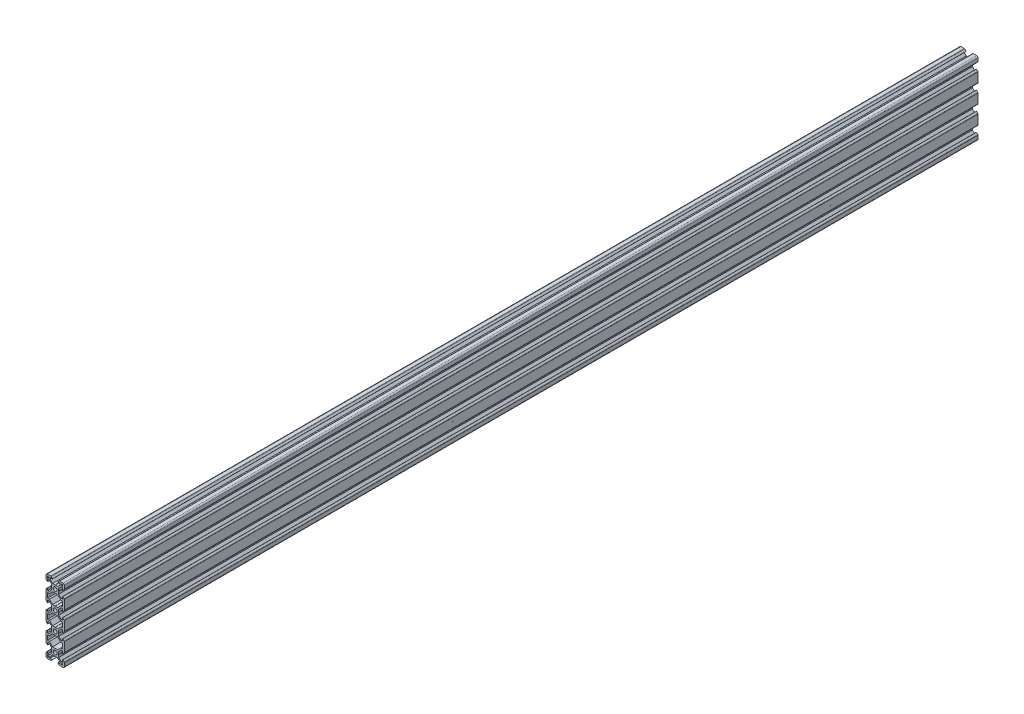
SolidWorks part; units mm, degrees
ref_plane "Front Plane" through (0, 0, 0) normal (0, 0, 1) x (1, 0, 0)
ref_plane "Top Plane" through (0, 0, 0) normal (0, 1, 0) x (1, 0, 0)
ref_plane "Right Plane" through (0, 0, 0) normal (1, 0, 0) x (0, 0, -1)
sketch "Sketch2" plane through (0, 0, 0) normal (0, 0, 1) x (1, 0, 0)
  line L0 (-8.2, 2.8875) -> (-8.2, 5.4975)
  line L3 (-4.9072, 9.9975) -> (-8.5, 9.9975)
  line L4 (-10, 4.9047) -> (-10, 8.4975)
  line L5 (-2.1, 0) -> (-3.8, 0) construction
  line L6 (0, 3.8) -> (0, 2.1) construction
  line L7 (-0.1, 3.9) -> (-2.8404, 3.9)
  line L8 (-3.9, 0.1) -> (-3.9, 2.8383)
  line L9 (-2.89, 8.1975) -> (-5.5, 8.1975)
  line L10 (-6.57, 8.1975) -> (-6.57, 7.6575)
  line L11 (-8.2, 6.5675) -> (-7.66, 6.5675)
  line L12 (-5.5, 8.1975) -> (-5.5, 6.5588)
  line L13 (-6.56, 5.4975) -> (-8.2, 5.4975)
  line L14 (-8.2, 8.1975) -> (-1.4852, 1.4847) construction
  line L15 (-6.56, 5.4975) -> (-3.9, 2.8383)
  line L16 (-5.5, 6.5588) -> (-2.8404, 3.9)
  line L17 (-7.66, 6.5675) -> (-6.57, 7.6575)
  line L18 (-8.7302, 7.6671) -> (-0.5302, -0.5304) construction
  line L19 (-7.6698, 8.7279) -> (0.5302, 0.5304) construction
  line L20 (-8.2, 8.1975) -> (0, 0) construction
  line L21 (-8.2, 6.5675) -> (-8.2, 8.1975)
  line L22 (-8.2, -0.0025) -> (-8.2, 8.1975) construction
  line L23 (-6.57, 8.1975) -> (-8.2, 8.1975)
  line L24 (0, 8.1975) -> (-8.2, 8.1975) construction
  line L25 (-10, -0.0025) -> (-10, 9.9975) construction
  line L26 (0, 9.9975) -> (-10, 9.9975) construction
  line L27 (-2.89, 8.3075) -> (-2.89, 8.1975)
  line L29 (-8.31, 2.8875) -> (-8.2, 2.8875)
  line L30 (-4.3486, 9.7661) -> (-2.89, 8.3075)
  line L31 (-8.31, 2.8875) -> (-9.7686, 4.3461)
  line L34 (-0.1, 3.9) -> (0, 3.8)
  line L35 (-3.9, 0.1) -> (-3.8, 0)
  line L36 (-10, -20) -> (0, -20) construction
  line L37 (0, 0) -> (0, -20) construction
  line L38 (0, -3.9) -> (-2.8404, -3.9)
  line L39 (-3.8, 0) -> (-3.9, -0.1)
  line L40 (-3.9, -0.1) -> (-3.9, -2.84)
  line L41 (-2.8404, -3.9) -> (-6.25, -7.3096)
  line L42 (-3.9, -2.84) -> (-6.56, -5.5)
  line L43 (-8.21, -2.89) -> (-8.21, -5.5)
  line L44 (-6.56, 5.4975) -> (-6.56, -5.5) construction
  line L45 (-6.56, -5.5) -> (-8.21, -5.5)
  line L46 (-6.25, -7.3096) -> (-6.25, -12.7) construction
  line L47 (-6.25, -7.3096) -> (-8.21, -7.3096)
  line L48 (-8.21, -2.89) -> (-8.31, -2.89)
  line L49 (-8.31, -2.89) -> (-9.7657, -4.3457)
  line L51 (-8.21, -7.3096) -> (-8.21, -12.7)
  line L52 (-0.1, -16.1) -> (-2.85, -16.1)
  line L53 (-3.9, -17.16) -> (-3.9, -19.9)
  line L54 (-6.25, -12.7) -> (-2.85, -16.1)
  line L58 (-3.9, -17.16) -> (-6.56, -14.5)
  line L60 (-8.21, -17.11) -> (-8.31, -17.11)
  line L61 (-10, -4.9114) -> (-10, -15.0886)
  line L62 (-9.7657, -15.6543) -> (-8.31, -17.11)
  line L63 (-0.1, -16.1) -> (0, -16.2)
  line L64 (-3.9, -19.9) -> (-3.8, -20)
  line L65 (-8.21, -14.5) -> (-6.56, -14.5)
  line L66 (-8.21, -12.7) -> (-6.25, -12.7)
  line L67 (-10, -30.01) -> (0, -30.01) construction
  line L68 (-8.21, -14.5) -> (-8.21, -17.11)
  line L69 (-3.9, -20.1) -> (-3.8, -20)
  line L71 (-10, -20) -> (0, -20) construction
  line L72 (-8.21, -30.01) -> (-8.21, -27.31)
  line L73 (-10, -30.01) -> (-10, -24.9101)
  line L74 (-8.21, -25.4987) -> (-8.21, -22.8887)
  line L76 (-8.21, -27.31) -> (-6.25, -27.31)
  line L77 (-8.21, -25.4987) -> (-6.56, -25.4987)
  line L85 (-0.1, -23.9) -> (0, -23.8)
  line L95 (-9.7657, -24.3444) -> (-8.31, -22.8887)
  line L96 (-8.21, -22.8887) -> (-8.31, -22.8887)
  line L97 (-3.9, -22.8387) -> (-6.56, -25.4987)
  line L98 (-6.25, -27.31) -> (-2.84, -23.9)
  line L99 (-3.9, -22.8387) -> (-3.9, -20.1)
  line L100 (-0.1, -23.9) -> (-2.84, -23.9)
  arc A1 (-10, 8.4975) -> (-8.5, 9.9975) centre (-8.5, 8.4975) cw
  arc A2 (-9.7686, 4.3461) -> (-10, 4.9047) centre (-9.21, 4.9047) cw
  arc A3 (-4.3486, 9.7661) -> (-4.9072, 9.9975) centre (-4.9072, 9.2075) ccw
  arc A5 (0, 2.1) -> (0, -2.1) centre (0, 0) ccw
  arc A6 (-9.7657, -15.6543) -> (-10, -15.0886) centre (-9.2, -15.0886) cw
  arc A7 (-9.7657, -4.3457) -> (-10, -4.9114) centre (-9.2, -4.9114) ccw
  arc A8 (0, -17.9) -> (0, -22.1) centre (0, -20) ccw
  arc A10 (-9.7657, -24.3444) -> (-10, -24.9101) centre (-9.2, -24.9101) ccw
  point P29 (-10, 9.9975)
  point P39 (-10, 4.5775)
  point P42 (-4.58, 9.9975)
  point P76 (-10, -15.42)
  point P79 (-10, -4.58)
  dimension "D15" = 1.5
  dimension "D22" = 0.79
  dimension "D30" = 2.1
  dimension "D31" = 2.1
  dimension "D51" = 0.8
  dimension "D52" = 2.61
  dimension "D64" = 1.65
  dimension "D53" = 0.8
  dimension "D55" = 3.9
  dimension "D4" = 1.8
  dimension "D5" = 3.43
  dimension "D6" = 3.43
  dimension "D7" = 0.54
  dimension "D8" = 0.54
  dimension "D9" = 1.07
  dimension "D10" = 1.07
  dimension "D11" = 3.9
  dimension "D12" = 3.9
  dimension "D16" = 7.11
  dimension "D17" = 0.11
  dimension "D18" = 1.69
  dimension "D19" = 0.11
  dimension "D20" = 7.11
  dimension "D21" = 1.69
  dimension "D23" = 10
  dimension "D24" = 0.1
  dimension "D25" = 45
  dimension "D26" = 0.1
  dimension "D27" = 45
  dimension "D28" = 1.64
  dimension "D29" = 20
  dimension "D32" = 3.9
  dimension "D33" = 45
  dimension "D34" = 2.74
  dimension "D35" = 45
  dimension "D36" = 1.96
  dimension "D37" = 2.61
  dimension "D38" = 90
  dimension "D39" = 2.61
  dimension "D40" = 3.9
  dimension "D41" = 3.9
  dimension "D42" = 135
  dimension "D44" = 45
  dimension "D45" = 1.8
  dimension "D46" = 0.1
  dimension "D47" = 0.1
  dimension "D48" = 45
  dimension "D49" = 0.1
  dimension "D50" = 45
  dimension "D43" = 5.5
  dimension "D54" = 3.9
  dimension "D56" = 45
  dimension "D57" = 2.7
  dimension "D59" = 45
  dimension "D60" = 0.1
  dimension "D61" = 0.1
  dimension "D62" = 45
  dimension "D63" = 2.84
  dimension "D65" = 1.96
  dimension "D66" = 45
  dimension "D67" = 1.5
  dimension "D13" = 0.75
  dimension "D14" = 0.75
sketch "Sketch3" plane through (0, 0, 0) normal (0, 0, 1) x (1, 0, 0)
  line L0 (-0.1, 3.9) -> (0, 3.8) construction
  line L1 (-0.1, 3.9) -> (-2.8404, 3.9) construction
  line L2 (-5.5, 6.5588) -> (-2.8404, 3.9) construction
  line L3 (-5.5, 8.1975) -> (-5.5, 6.5588) construction
  line L4 (-2.89, 8.1975) -> (-5.5, 8.1975) construction
  line L5 (-7.66, 6.5675) -> (-6.57, 7.6575)
  line L6 (-6.57, 7.6575) -> (-6.57, 8.1975)
  line L7 (-6.57, 8.1975) -> (-8.2, 8.1975)
  line L8 (-8.2, 8.1975) -> (-8.2, 6.5675)
  line L9 (-8.2, 6.5675) -> (-7.66, 6.5675)
  line L10 (-7.66, 6.5675) -> (-6.57, 7.6575)
  line L11 (-6.57, 7.6575) -> (-6.57, 8.1975)
  line L12 (-6.57, 8.1975) -> (-8.2, 8.1975)
  line L13 (-8.2, 8.1975) -> (-8.2, 6.5675)
  line L14 (-8.2, 6.5675) -> (-7.66, 6.5675)
  line L15 (-2.89, 8.3075) -> (-2.89, 8.1975) construction
  line L16 (-4.3486, 9.7661) -> (-2.89, 8.3075) construction
  line L17 (-4.9072, 9.9975) -> (-8.5, 9.9975) construction
  line L18 (-10, 4.9047) -> (-10, 8.4975) construction
  line L19 (-8.31, 2.8875) -> (-9.7686, 4.3461) construction
  line L20 (-8.31, 2.8875) -> (-8.2, 2.8875) construction
  line L21 (-8.2, 2.8875) -> (-8.2, 5.4975) construction
  line L22 (-6.56, 5.4975) -> (-8.2, 5.4975) construction
  line L23 (-6.56, 5.4975) -> (-3.9, 2.8383) construction
  line L24 (-3.9, 0.1) -> (-3.9, 2.8383) construction
  line L25 (-3.9, 0.1) -> (-3.8, 0) construction
  line L26 (-3.8, 0) -> (-3.9, -0.1) construction
  line L27 (-3.9, -0.1) -> (-3.9, -2.84) construction
  line L28 (-3.9, -2.84) -> (-6.56, -5.5) construction
  line L29 (-6.56, -5.5) -> (-8.21, -5.5) construction
  line L30 (-8.21, -2.89) -> (-8.21, -5.5) construction
  line L31 (-8.21, -2.89) -> (-8.31, -2.89) construction
  line L32 (-8.31, -2.89) -> (-9.7657, -4.3457) construction
  line L33 (-10, -4.9114) -> (-10, -15.0886) construction
  line L34 (-9.7657, -15.6543) -> (-8.31, -17.11) construction
  line L35 (-8.21, -17.11) -> (-8.31, -17.11) construction
  line L36 (-8.21, -14.5) -> (-8.21, -17.11) construction
  line L37 (-8.21, -14.5) -> (-6.56, -14.5) construction
  line L38 (-3.9, -17.16) -> (-6.56, -14.5) construction
  line L39 (-3.9, -17.16) -> (-3.9, -19.9) construction
  line L40 (-3.9, -19.9) -> (-3.8, -20) construction
  line L41 (-3.9, -20.1) -> (-3.8, -20) construction
  line L42 (-3.9, -22.8387) -> (-3.9, -20.1) construction
  line L43 (-3.9, -22.8387) -> (-6.56, -25.4987) construction
  line L44 (-8.21, -25.4987) -> (-6.56, -25.4987) construction
  line L45 (-8.21, -25.4987) -> (-8.21, -22.8887) construction
  line L46 (-8.21, -22.8887) -> (-8.31, -22.8887) construction
  line L47 (-9.7657, -24.3444) -> (-8.31, -22.8887) construction
  line L48 (-10, -30.01) -> (-10, -24.9101) construction
  line L49 (0, -3.9) -> (-2.8404, -3.9) construction
  line L50 (-2.8404, -3.9) -> (-6.25, -7.3096) construction
  line L51 (-6.25, -7.3096) -> (-8.21, -7.3096) construction
  line L52 (-8.21, -7.3096) -> (-8.21, -12.7) construction
  line L53 (-8.21, -12.7) -> (-6.25, -12.7) construction
  line L54 (-6.25, -12.7) -> (-2.85, -16.1) construction
  line L55 (-0.1, -16.1) -> (-2.85, -16.1) construction
  line L56 (-0.1, -16.1) -> (0, -16.2) construction
  line L57 (-0.1, -23.9) -> (0, -23.8) construction
  line L58 (-0.1, -23.9) -> (-2.84, -23.9) construction
  line L59 (-6.25, -27.31) -> (-2.84, -23.9) construction
  line L60 (-8.21, -27.31) -> (-6.25, -27.31) construction
  line L61 (-8.21, -30.01) -> (-8.21, -27.31) construction
  line L62 (-0.1, 3.9) -> (0, 3.8)
  line L63 (-0.1, 3.9) -> (-2.8404, 3.9)
  line L64 (-5.5, 6.5588) -> (-2.8404, 3.9)
  line L65 (-5.5, 8.1975) -> (-5.5, 6.5588)
  line L66 (-2.89, 8.1975) -> (-5.5, 8.1975)
  line L67 (-2.89, 8.3075) -> (-2.89, 8.1975)
  line L68 (-4.3486, 9.7661) -> (-2.89, 8.3075)
  line L69 (-4.9072, 9.9975) -> (-8.5, 9.9975)
  line L70 (-10, 4.9047) -> (-10, 8.4975)
  line L71 (-8.31, 2.8875) -> (-9.7686, 4.3461)
  line L72 (-8.31, 2.8875) -> (-8.2, 2.8875)
  line L73 (-8.2, 2.8875) -> (-8.2, 5.4975)
  line L74 (-6.56, 5.4975) -> (-8.2, 5.4975)
  line L75 (-6.56, 5.4975) -> (-3.9, 2.8383)
  line L76 (-3.9, 0.1) -> (-3.9, 2.8383)
  line L77 (-3.9, 0.1) -> (-3.8, 0)
  line L78 (-3.8, 0) -> (-3.9, -0.1)
  line L79 (-3.9, -0.1) -> (-3.9, -2.84)
  line L80 (-3.9, -2.84) -> (-6.56, -5.5)
  line L81 (-6.56, -5.5) -> (-8.21, -5.5)
  line L82 (-8.21, -2.89) -> (-8.21, -5.5)
  line L83 (-8.21, -2.89) -> (-8.31, -2.89)
  line L84 (-8.31, -2.89) -> (-9.7657, -4.3457)
  line L85 (-10, -4.9114) -> (-10, -15.0886)
  line L86 (-9.7657, -15.6543) -> (-8.31, -17.11)
  line L87 (-8.21, -17.11) -> (-8.31, -17.11)
  line L88 (-8.21, -14.5) -> (-8.21, -17.11)
  line L89 (-8.21, -14.5) -> (-6.56, -14.5)
  line L90 (-3.9, -17.16) -> (-6.56, -14.5)
  line L91 (-3.9, -17.16) -> (-3.9, -19.9)
  line L92 (-3.9, -19.9) -> (-3.8, -20)
  line L93 (-3.9, -20.1) -> (-3.8, -20)
  line L94 (-3.9, -22.8387) -> (-3.9, -20.1)
  line L95 (-3.9, -22.8387) -> (-6.56, -25.4987)
  line L96 (-8.21, -25.4987) -> (-6.56, -25.4987)
  line L97 (-8.21, -25.4987) -> (-8.21, -22.8887)
  line L98 (-8.21, -22.8887) -> (-8.31, -22.8887)
  line L99 (-9.7657, -24.3444) -> (-8.31, -22.8887)
  line L100 (-10, -35.1099) -> (-10, -24.9101)
  line L101 (2.8404, -3.9) -> (-2.8404, -3.9)
  line L102 (-2.8404, -3.9) -> (-6.25, -7.3096)
  line L103 (-6.25, -7.3096) -> (-8.21, -7.3096)
  line L104 (-8.21, -7.3096) -> (-8.21, -12.7)
  line L105 (-8.21, -12.7) -> (-6.25, -12.7)
  line L106 (-6.25, -12.7) -> (-2.85, -16.1)
  line L107 (-0.1, -16.1) -> (-2.85, -16.1)
  line L108 (-0.1, -16.1) -> (0, -16.2)
  line L109 (-0.1, -23.9) -> (0, -23.8)
  line L110 (-0.1, -23.9) -> (-2.84, -23.9)
  line L111 (-6.25, -27.31) -> (-2.84, -23.9)
  line L112 (-8.21, -27.31) -> (-6.25, -27.31)
  line L113 (-8.21, -32.71) -> (-8.21, -27.31)
  line L114 (0, 0) -> (0, -20) construction
  line L115 (-10, -30.01) -> (0, -30.01) construction
  line L116 (0, 0) -> (0, -20) construction
  line L117 (-10, -30.01) -> (10, -30.01) construction
  line L118 (8.21, -32.71) -> (8.21, -27.31)
  line L119 (8.21, -27.31) -> (6.25, -27.31)
  line L120 (6.25, -27.31) -> (2.84, -23.9)
  line L121 (0.1, -23.9) -> (2.84, -23.9)
  line L122 (0.1, -23.9) -> (0, -23.8)
  line L123 (0.1, -16.1) -> (0, -16.2)
  line L124 (0.1, -16.1) -> (2.85, -16.1)
  line L125 (6.25, -12.7) -> (2.85, -16.1)
  line L126 (8.21, -12.7) -> (6.25, -12.7)
  line L127 (8.21, -7.3096) -> (8.21, -12.7)
  line L128 (6.25, -7.3096) -> (8.21, -7.3096)
  line L129 (2.8404, -3.9) -> (6.25, -7.3096)
  line L130 (10, -35.1099) -> (10, -24.9101)
  line L131 (9.7657, -24.3444) -> (8.31, -22.8887)
  line L132 (8.21, -22.8887) -> (8.31, -22.8887)
  line L133 (8.21, -25.4987) -> (8.21, -22.8887)
  line L134 (8.21, -25.4987) -> (6.56, -25.4987)
  line L135 (3.9, -22.8387) -> (6.56, -25.4987)
  line L136 (3.9, -22.8387) -> (3.9, -20.1)
  line L137 (3.9, -20.1) -> (3.8, -20)
  line L138 (3.9, -19.9) -> (3.8, -20)
  line L139 (3.9, -17.16) -> (3.9, -19.9)
  line L140 (3.9, -17.16) -> (6.56, -14.5)
  line L141 (8.21, -14.5) -> (6.56, -14.5)
  line L142 (8.21, -14.5) -> (8.21, -17.11)
  line L143 (8.21, -17.11) -> (8.31, -17.11)
  line L144 (9.7657, -15.6543) -> (8.31, -17.11)
  line L145 (10, -4.9114) -> (10, -15.0886)
  line L146 (8.31, -2.89) -> (9.7657, -4.3457)
  line L147 (8.21, -2.89) -> (8.31, -2.89)
  line L148 (8.21, -2.89) -> (8.21, -5.5)
  line L149 (6.56, -5.5) -> (8.21, -5.5)
  line L150 (3.9, -2.84) -> (6.56, -5.5)
  line L151 (3.9, -0.1) -> (3.9, -2.84)
  line L152 (3.8, 0) -> (3.9, -0.1)
  line L153 (3.9, 0.1) -> (3.8, 0)
  line L154 (3.9, 0.1) -> (3.9, 2.8383)
  line L155 (6.56, 5.4975) -> (3.9, 2.8383)
  line L156 (6.56, 5.4975) -> (8.2, 5.4975)
  line L157 (8.2, 2.8875) -> (8.2, 5.4975)
  line L158 (8.31, 2.8875) -> (8.2, 2.8875)
  line L159 (8.31, 2.8875) -> (9.7686, 4.3461)
  line L160 (10, 4.9047) -> (10, 8.4975)
  line L161 (4.9072, 9.9975) -> (8.5, 9.9975)
  line L162 (4.3486, 9.7661) -> (2.89, 8.3075)
  line L163 (2.89, 8.3075) -> (2.89, 8.1975)
  line L164 (2.89, 8.1975) -> (5.5, 8.1975)
  line L165 (5.5, 8.1975) -> (5.5, 6.5588)
  line L166 (5.5, 6.5588) -> (2.8404, 3.9)
  line L167 (0.1, 3.9) -> (2.8404, 3.9)
  line L168 (0.1, 3.9) -> (0, 3.8)
  line L169 (8.2, 6.5675) -> (7.66, 6.5675)
  line L170 (8.2, 8.1975) -> (8.2, 6.5675)
  line L171 (6.57, 8.1975) -> (8.2, 8.1975)
  line L172 (6.57, 7.6575) -> (6.57, 8.1975)
  line L173 (7.66, 6.5675) -> (6.57, 7.6575)
  line L174 (0, -60.02) -> (0, -40.02) construction
  line L175 (7.66, -66.5875) -> (6.57, -67.6775)
  line L176 (6.57, -67.6775) -> (6.57, -68.2175)
  line L177 (6.57, -68.2175) -> (8.2, -68.2175)
  line L178 (8.2, -68.2175) -> (8.2, -66.5875)
  line L179 (8.2, -66.5875) -> (7.66, -66.5875)
  line L180 (0.1, -63.92) -> (0, -63.82)
  line L181 (0.1, -63.92) -> (2.8404, -63.92)
  line L182 (5.5, -66.5788) -> (2.8404, -63.92)
  line L183 (5.5, -68.2175) -> (5.5, -66.5788)
  line L184 (2.89, -68.2175) -> (5.5, -68.2175)
  line L185 (2.89, -68.3275) -> (2.89, -68.2175)
  line L186 (4.3486, -69.7861) -> (2.89, -68.3275)
  line L187 (4.9072, -70.0175) -> (8.5, -70.0175)
  line L188 (10, -64.9247) -> (10, -68.5175)
  line L189 (8.31, -62.9075) -> (9.7686, -64.3661)
  line L190 (8.31, -62.9075) -> (8.2, -62.9075)
  line L191 (8.2, -62.9075) -> (8.2, -65.5175)
  line L192 (6.56, -65.5175) -> (8.2, -65.5175)
  line L193 (6.56, -65.5175) -> (3.9, -62.8583)
  line L194 (3.9, -60.12) -> (3.9, -62.8583)
  line L195 (3.9, -60.12) -> (3.8, -60.02)
  line L196 (3.8, -60.02) -> (3.9, -59.92)
  line L197 (3.9, -59.92) -> (3.9, -57.18)
  line L198 (3.9, -57.18) -> (6.56, -54.52)
  line L199 (6.56, -54.52) -> (8.21, -54.52)
  line L200 (8.21, -57.13) -> (8.21, -54.52)
  line L201 (8.21, -57.13) -> (8.31, -57.13)
  line L202 (8.31, -57.13) -> (9.7657, -55.6743)
  line L203 (10, -55.1086) -> (10, -44.9314)
  line L204 (9.7657, -44.3657) -> (8.31, -42.91)
  line L205 (8.21, -42.91) -> (8.31, -42.91)
  line L206 (8.21, -45.52) -> (8.21, -42.91)
  line L207 (8.21, -45.52) -> (6.56, -45.52)
  line L208 (3.9, -42.86) -> (6.56, -45.52)
  line L209 (3.9, -42.86) -> (3.9, -40.12)
  line L210 (3.9, -40.12) -> (3.8, -40.02)
  line L211 (3.9, -39.92) -> (3.8, -40.02)
  line L212 (3.9, -37.1813) -> (3.9, -39.92)
  line L213 (3.9, -37.1813) -> (6.56, -34.5213)
  line L214 (8.21, -34.5213) -> (6.56, -34.5213)
  line L215 (8.21, -34.5213) -> (8.21, -37.1313)
  line L216 (8.21, -37.1313) -> (8.31, -37.1313)
  line L217 (9.7657, -35.6756) -> (8.31, -37.1313)
  line L218 (2.8404, -56.12) -> (6.25, -52.7104)
  line L219 (6.25, -52.7104) -> (8.21, -52.7104)
  line L220 (8.21, -52.7104) -> (8.21, -47.32)
  line L221 (8.21, -47.32) -> (6.25, -47.32)
  line L222 (6.25, -47.32) -> (2.85, -43.92)
  line L223 (0.1, -43.92) -> (2.85, -43.92)
  line L224 (0.1, -43.92) -> (0, -43.82)
  line L225 (0.1, -36.12) -> (0, -36.22)
  line L226 (0.1, -36.12) -> (2.84, -36.12)
  line L227 (6.25, -32.71) -> (2.84, -36.12)
  line L228 (8.21, -32.71) -> (6.25, -32.71)
  line L229 (-8.21, -32.71) -> (-6.25, -32.71)
  line L230 (-6.25, -32.71) -> (-2.84, -36.12)
  line L231 (-0.1, -36.12) -> (-2.84, -36.12)
  line L232 (-0.1, -36.12) -> (0, -36.22)
  line L233 (-0.1, -43.92) -> (0, -43.82)
  line L234 (-0.1, -43.92) -> (-2.85, -43.92)
  line L235 (-6.25, -47.32) -> (-2.85, -43.92)
  line L236 (-8.21, -47.32) -> (-6.25, -47.32)
  line L237 (-8.21, -52.7104) -> (-8.21, -47.32)
  line L238 (-6.25, -52.7104) -> (-8.21, -52.7104)
  line L239 (-2.8404, -56.12) -> (-6.25, -52.7104)
  line L240 (2.8404, -56.12) -> (-2.8404, -56.12)
  line L241 (-9.7657, -35.6756) -> (-8.31, -37.1313)
  line L242 (-8.21, -37.1313) -> (-8.31, -37.1313)
  line L243 (-8.21, -34.5213) -> (-8.21, -37.1313)
  line L244 (-8.21, -34.5213) -> (-6.56, -34.5213)
  line L245 (-3.9, -37.1813) -> (-6.56, -34.5213)
  line L246 (-3.9, -37.1813) -> (-3.9, -39.92)
  line L247 (-3.9, -39.92) -> (-3.8, -40.02)
  line L248 (-3.9, -40.12) -> (-3.8, -40.02)
  line L249 (-3.9, -42.86) -> (-3.9, -40.12)
  line L250 (-3.9, -42.86) -> (-6.56, -45.52)
  line L251 (-8.21, -45.52) -> (-6.56, -45.52)
  line L252 (-8.21, -45.52) -> (-8.21, -42.91)
  line L253 (-8.21, -42.91) -> (-8.31, -42.91)
  line L254 (-9.7657, -44.3657) -> (-8.31, -42.91)
  line L255 (-10, -55.1086) -> (-10, -44.9314)
  line L256 (-8.31, -57.13) -> (-9.7657, -55.6743)
  line L257 (-8.21, -57.13) -> (-8.31, -57.13)
  line L258 (-8.21, -57.13) -> (-8.21, -54.52)
  line L259 (-6.56, -54.52) -> (-8.21, -54.52)
  line L260 (-3.9, -57.18) -> (-6.56, -54.52)
  line L261 (-3.9, -59.92) -> (-3.9, -57.18)
  line L262 (-3.8, -60.02) -> (-3.9, -59.92)
  line L263 (-3.9, -60.12) -> (-3.8, -60.02)
  line L264 (-3.9, -60.12) -> (-3.9, -62.8583)
  line L265 (-6.56, -65.5175) -> (-3.9, -62.8583)
  line L266 (-6.56, -65.5175) -> (-8.2, -65.5175)
  line L267 (-8.2, -62.9075) -> (-8.2, -65.5175)
  line L268 (-8.31, -62.9075) -> (-8.2, -62.9075)
  line L269 (-8.31, -62.9075) -> (-9.7686, -64.3661)
  line L270 (-10, -64.9247) -> (-10, -68.5175)
  line L271 (-4.9072, -70.0175) -> (-8.5, -70.0175)
  line L272 (-4.3486, -69.7861) -> (-2.89, -68.3275)
  line L273 (-2.89, -68.3275) -> (-2.89, -68.2175)
  line L274 (-2.89, -68.2175) -> (-5.5, -68.2175)
  line L275 (-5.5, -68.2175) -> (-5.5, -66.5788)
  line L276 (-5.5, -66.5788) -> (-2.8404, -63.92)
  line L277 (-0.1, -63.92) -> (-2.8404, -63.92)
  line L278 (-0.1, -63.92) -> (0, -63.82)
  line L279 (-8.2, -66.5875) -> (-7.66, -66.5875)
  line L280 (-8.2, -68.2175) -> (-8.2, -66.5875)
  line L281 (-6.57, -68.2175) -> (-8.2, -68.2175)
  line L282 (-6.57, -67.6775) -> (-6.57, -68.2175)
  line L283 (-7.66, -66.5875) -> (-6.57, -67.6775)
  arc A0 (0, 2.1) -> (0, -2.1) centre (0, 0) ccw construction
  arc A1 (0, -17.9) -> (0, -22.1) centre (0, -20) ccw construction
  arc A2 (-4.3486, 9.7661) -> (-4.9072, 9.9975) centre (-4.9072, 9.2075) ccw construction
  arc A3 (-8.5, 9.9975) -> (-10, 8.4975) centre (-8.5, 8.4975) ccw construction
  arc A4 (-10, 4.9047) -> (-9.7686, 4.3461) centre (-9.21, 4.9047) ccw construction
  arc A5 (-9.7657, -4.3457) -> (-10, -4.9114) centre (-9.2, -4.9114) ccw construction
  arc A6 (-10, -15.0886) -> (-9.7657, -15.6543) centre (-9.2, -15.0886) ccw construction
  arc A7 (-9.7657, -24.3444) -> (-10, -24.9101) centre (-9.2, -24.9101) ccw construction
  circle A8 centre (0, 0) radius 2.1
  circle A9 centre (0, -20) radius 2.1
  arc A10 (-4.3486, 9.7661) -> (-4.9072, 9.9975) centre (-4.9072, 9.2075) ccw
  arc A11 (-8.5, 9.9975) -> (-10, 8.4975) centre (-8.5, 8.4975) ccw
  arc A12 (-10, 4.9047) -> (-9.7686, 4.3461) centre (-9.21, 4.9047) ccw
  arc A13 (-9.7657, -4.3457) -> (-10, -4.9114) centre (-9.2, -4.9114) ccw
  arc A14 (-10, -15.0886) -> (-9.7657, -15.6543) centre (-9.2, -15.0886) ccw
  arc A15 (-9.7657, -24.3444) -> (-10, -24.9101) centre (-9.2, -24.9101) ccw
  arc A16 (9.7657, -24.3444) -> (10, -24.9101) centre (9.2, -24.9101) cw
  arc A17 (10, -15.0886) -> (9.7657, -15.6543) centre (9.2, -15.0886) cw
  arc A18 (9.7657, -4.3457) -> (10, -4.9114) centre (9.2, -4.9114) cw
  arc A19 (10, 4.9047) -> (9.7686, 4.3461) centre (9.21, 4.9047) cw
  arc A20 (8.5, 9.9975) -> (10, 8.4975) centre (8.5, 8.4975) cw
  arc A21 (4.3486, 9.7661) -> (4.9072, 9.9975) centre (4.9072, 9.2075) cw
  arc A22 (4.3486, -69.7861) -> (4.9072, -70.0175) centre (4.9072, -69.2275) ccw
  arc A23 (8.5, -70.0175) -> (10, -68.5175) centre (8.5, -68.5175) ccw
  arc A24 (10, -64.9247) -> (9.7686, -64.3661) centre (9.21, -64.9247) ccw
  arc A25 (9.7657, -55.6743) -> (10, -55.1086) centre (9.2, -55.1086) ccw
  arc A26 (10, -44.9314) -> (9.7657, -44.3657) centre (9.2, -44.9314) ccw
  arc A27 (9.7657, -35.6756) -> (10, -35.1099) centre (9.2, -35.1099) ccw
  arc A28 (-9.7657, -35.6756) -> (-10, -35.1099) centre (-9.2, -35.1099) cw
  arc A29 (-10, -44.9314) -> (-9.7657, -44.3657) centre (-9.2, -44.9314) cw
  arc A30 (-9.7657, -55.6743) -> (-10, -55.1086) centre (-9.2, -55.1086) cw
  arc A31 (-10, -64.9247) -> (-9.7686, -64.3661) centre (-9.21, -64.9247) cw
  arc A32 (-8.5, -70.0175) -> (-10, -68.5175) centre (-8.5, -68.5175) cw
  arc A33 (-4.3486, -69.7861) -> (-4.9072, -70.0175) centre (-4.9072, -69.2275) cw
  circle A34 centre (0, -40.02) radius 2.1
  circle A35 centre (0, -60.02) radius 2.1
  point P240 (8.21, -30.01)
  point P288 (-0.1, 9.9975)
  point P289 (0, -70.0175)
  point P290 (-10, -60.02)
  point P291 (10, -60.02)
  point P292 (10, -40.02)
  point P293 (-10, -40.02)
  point P294 (-10, -20)
  point P295 (10, -20)
  point P296 (10, 0)
  point P297 (-10, 0)
  point P298 (-45.6583, 8.4975)
  dimension "D1" = 0
extrude "Boss-Extrude1" add sketch "Sketch3" against normal blind 1000
